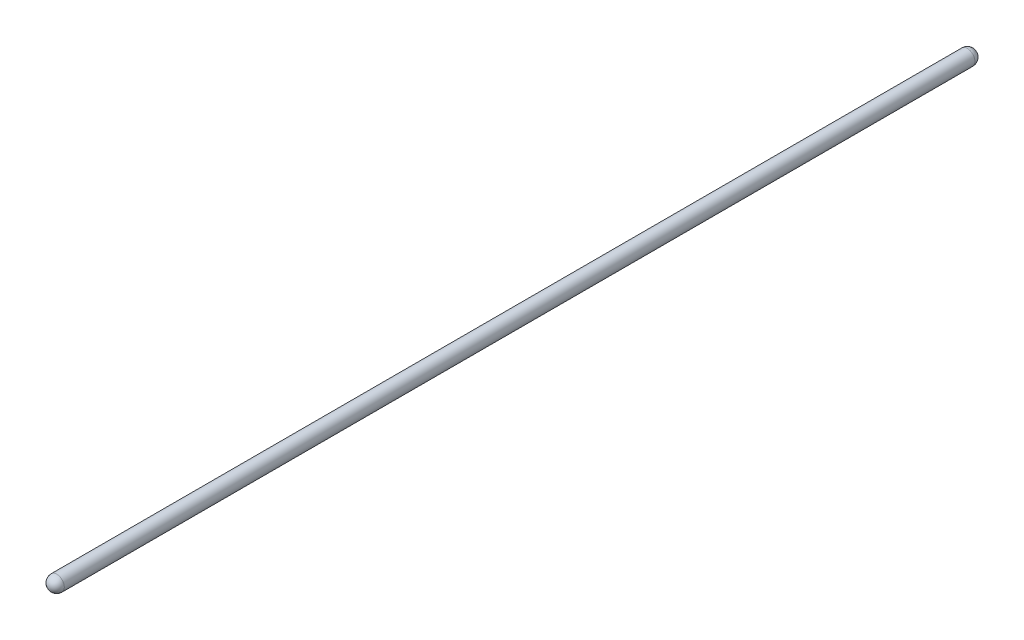
SolidWorks part; units mm, degrees
ref_plane "Front Plane" through (0, 0, 0) normal (0, 0, 1) x (1, 0, 0)
ref_plane "Top Plane" through (0, 0, 0) normal (0, 1, 0) x (1, 0, 0)
ref_plane "Right Plane" through (0, 0, 0) normal (1, 0, 0) x (0, 0, -1)
sketch "Sketch3" plane through (0, 0, 0) normal (0, 0, 1) x (1, 0, 0)
  circle A0 centre (0, 0) radius 5
  dimension "D1" = 10
extrude "Boss-Extrude1" add sketch "Sketch3" along normal blind 300
sketch "Sketch4" plane through (0, 0, 300) normal (0, 0, 1) x (1, 0, 0)
  line L0 (0, 5) -> (0, -5)
  arc A0 (0, 5) -> (0, -5) centre (0, 0) ccw
  circle A1 centre (0, 0) radius 5 construction
revolve "Revolve3" add sketch "Sketch4" angle 180 about L0
mirror "Mirror2" about plane through (0, 0, 0) normal (0, 0, 1) of "Boss-Extrude1", "Revolve3"
